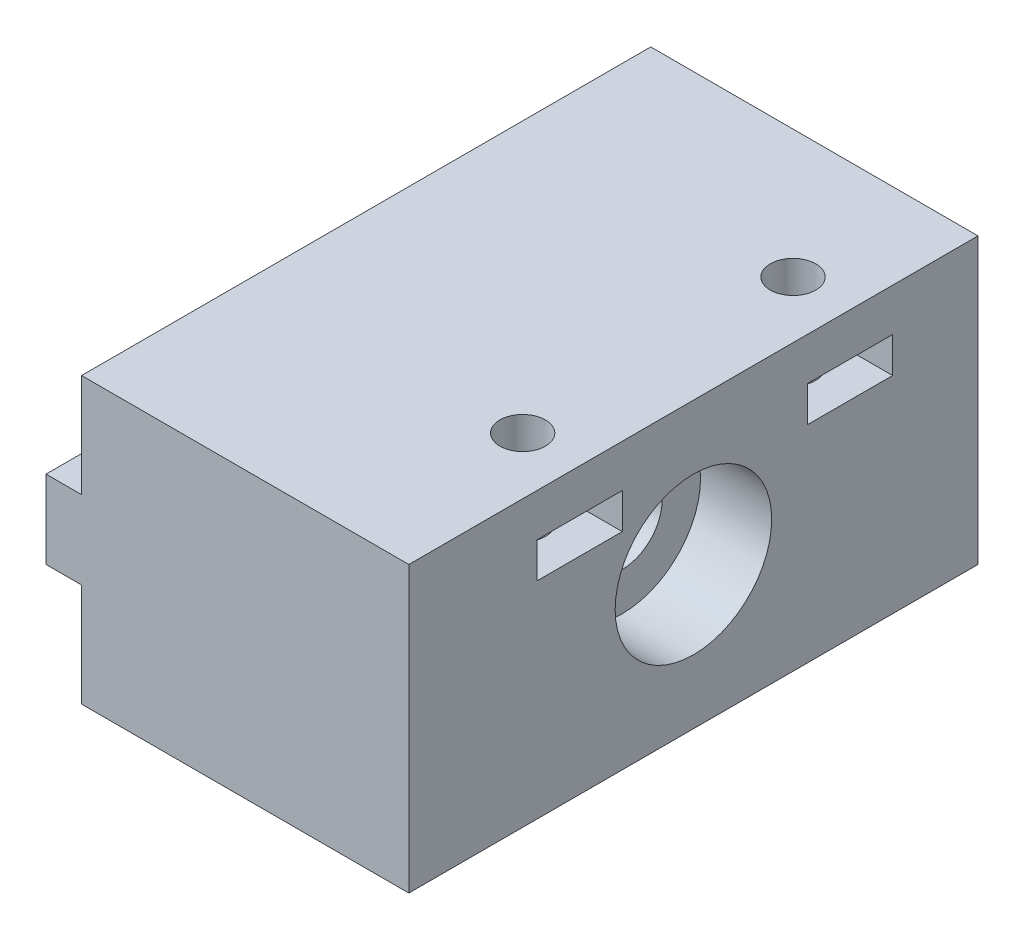
SolidWorks part; units mm, degrees
ref_plane "Front Plane" through (0, 0, 0) normal (0, 0, 1) x (1, 0, 0)
ref_plane "Top Plane" through (0, 0, 0) normal (0, 1, 0) x (1, 0, 0)
ref_plane "Right Plane" through (0, 0, 0) normal (1, 0, 0) x (0, 0, -1)
sketch "Sketch1" plane through (0, 0, 0) normal (0, 1, 0) x (1, 0, 0)
  line L1 (-0.6968, 0) -> (22.3032, 0)
  line L2 (-0.6968, 0) -> (-0.6968, 40)
  line L3 (-0.6968, 40) -> (22.3032, 40)
  line L4 (22.3032, 0) -> (22.3032, 40)
  dimension "D1" = 40
  dimension "D2" = 23
extrude "Boss-Extrude1" add sketch "Sketch1" along normal blind 20
sketch "Sketch5" plane through (0, 20, 0) normal (0, 1, 0) x (1, 0, 0)
  line L0 (22.3032, 0) -> (22.3032, 40) construction
  line L1 (-0.6968, 0) -> (22.3032, 0) construction
  circle A0 centre (18.3032, 12) radius 1.6
  circle A1 centre (18.3032, 31) radius 1.6
  dimension "D1" = 3.2
  dimension "D2" = 3.2
  dimension "D3" = 4
  dimension "D4" = 4
  dimension "D5" = 19
  dimension "D6" = 12
extrude "Cut-Extrude3" cut sketch "Sketch5" against normal through all
sketch "Sketch6" plane through (22.3032, 0, 0) normal (1, 0, 0) x (0, 0, -1)
  line L0 (0, 20) -> (40, 20) construction
  line L1 (9, 17) -> (15, 17)
  line L2 (9, 17) -> (9, 14.5)
  line L3 (9, 14.5) -> (15, 14.5)
  line L4 (15, 17) -> (15, 14.5)
  line L5 (28, 17) -> (34, 17)
  line L6 (28, 17) -> (28, 14.5)
  line L7 (28, 14.5) -> (34, 14.5)
  line L8 (34, 17) -> (34, 14.5)
  line L9 (0, 20) -> (0, 0) construction
  dimension "D1" = 2.5
  dimension "D2" = 6
  dimension "D3" = 2.5
  dimension "D4" = 6
  dimension "D5" = 9
  dimension "D6" = 19
  dimension "D7" = 3
  dimension "D8" = 3
extrude "Cut-Extrude4" cut sketch "Sketch6" against normal blind 8
sketch "Sketch7" plane through (-0.6968, 0, 0) normal (-1, 0, 0) x (0, 0, 1)
  line L0 (-40, 20) -> (0, 20) construction
  line L1 (-40, 20) -> (-40, 0) construction
  circle A0 centre (-20, 10) radius 2.8
  dimension "D1" = 5.6
  dimension "D2" = 10
  dimension "D3" = 20
extrude "Cut-Extrude5" cut sketch "Sketch7" against normal through all
sketch "Sketch8" plane through (22.3032, 0, 0) normal (1, 0, 0) x (0, 0, -1)
  circle A0 centre (20, 10) radius 5.5
  dimension "D1" = 11
extrude "Cut-Extrude6" cut sketch "Sketch8" against normal blind 5
sketch "Sketch9" plane through (-0.6968, 0, 0) normal (-1, 0, 0) x (0, 0, 1)
  line L0 (-40, 20) -> (-40, 0) construction
  line L1 (-40, 12.75) -> (-27, 12.75)
  line L2 (-40, 12.75) -> (-40, 7.25)
  line L3 (-40, 7.25) -> (-27, 7.25)
  line L4 (0, 12.75) -> (0, 7.25)
  line L5 (0, 20) -> (0, 0) construction
  line L6 (-40, 20) -> (0, 20) construction
  line L7 (-13, 12.75) -> (0, 12.75)
  line L9 (-27, 12.75) -> (-27, 7.25)
  line L11 (-13, 12.75) -> (-13, 7.25)
  line L12 (-13, 7.25) -> (0, 7.25)
  dimension "D1" = 5.5
  dimension "D2" = 7.25
  dimension "D3" = 14
  dimension "D4" = 13
extrude "Boss-Extrude6" add sketch "Sketch9" along normal blind 2.5
